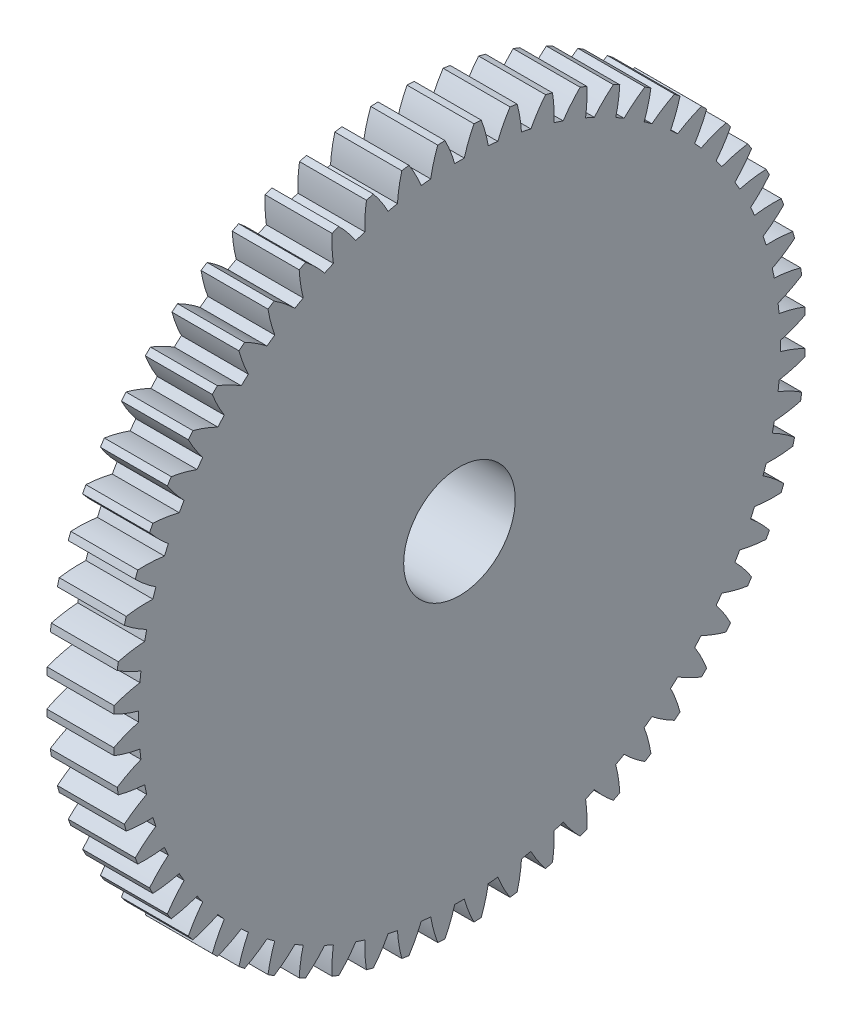
SolidWorks part; units mm, degrees
material "铜"
ref_plane "Plane1" through (0, 0, 0) normal (0, 0, 1) x (1, 0, 0)
ref_plane "Plane2" through (0, 0, 0) normal (0, 1, 0) x (1, 0, 0)
ref_plane "Plane3" through (0, 0, 0) normal (1, 0, 0) x (0, 0, -1)
sketch "HoldingSke" plane through (0, 0, 0) normal (0, 1, 0) x (1, 0, 0)
  line L0 (0, 0) -> (1, -1.7321)
  line L1 (-15, 0) -> (100, 0) construction
  line L2 (0, 0) -> (-2.1039, 2.3779)
  line L3 (0, 0) -> (-11.863, 4.5341)
  line L4 (0, 0) -> (4.318, 7.479)
  line L5 (0, 0) -> (-7.4956, -2.7956)
  line L6 (0, 0) -> (-2.4869, -1.6779)
  line L7 (-2.1039, 2.3779) -> (-0.3819, 10.1904)
  line L8 (-76.2, 54.61) -> (-75.3, 54.61)
  line L9 (-71.009, 38.7566) -> (-53.1078, 45.2721)
  line L10 (-76.2, 71.12) -> (104.1128, 71.12)
  line L11 (0, 0) -> (-3, 0)
  line L12 (-76.2, 101.6) -> (-76.181, 101.6)
  line L13 (24.9733, 27.94) -> (52.9518, 28.4284)
  line L14 (24.9733, 27.94) -> (24.9743, 27.94)
  line L15 (24.9733, 27.94) -> (100.4006, 29.5858)
  line L16 (-63.627, -0.5) -> (-12.827, -0.5)
  circle A0 centre (0, 0) radius 2.5
  circle A1 centre (0, 0) radius 4.5
  circle A2 centre (0, 0) radius 4.5
  circle A3 centre (0, 0) radius 2.5
  dimension "MHD" = 9
  dimension "Hub_dia" = 9
  dimension "Bore" = 5
  dimension "MBD" = 5
  dimension "Num_teeth" = 60
  dimension "Pitch" = 2
  dimension "Overall_len" = 8
  dimension "Show_teeth" = 60
  dimension "Thickness" = 3
  dimension "OAL" = 8.0001
  dimension "T_dim" = 0.9
  dimension "Ap" = 20
  dimension "H" = 19.05
  dimension "Pitch_radius" = 180.3128
  dimension "Width" = 3
  dimension "Backlash" = 0.019
  dimension "Addendum_fac" = 1
  dimension "Dedendum_fac" = 1.25
  dimension "Clearance_fac" = 0.25
  dimension "Dedendum_add" = 0.001
  dimension "Module" = 0.5
sketch "BasProSke" plane through (0, 0, 0) normal (0, 1, 0) x (1, 0, 0)
  line L0 (-10, 0) -> (60, 0) construction
  line L1 (0, 0) -> (0, 15.5)
  line L2 (0, 0) -> (3, 0)
  line L3 (3, 0) -> (3, 15.5)
  line L4 (3, 15.5) -> (0, 15.5)
  dimension "Thickness" = 3
  dimension "Diameter" = 31
revolve "Base-Revolve" add sketch "BasProSke" angle 360 about L0
sketch "TooCutSke" plane through (0, 0, 0) normal (1, 0, 0) x (0, 0, -1)
  line L1 (0, 0) -> (0, 107) construction
  line L2 (0, 0) -> (-0.4259, 14.994) construction
  line L3 (0, 0) -> (-1.5696, 29.9503) construction
  line L4 (-0.4259, 14.994) -> (-0.7848, 14.9751) construction
  arc A0 (0.2149, 14.3724) -> (-0.2149, 14.3724) centre (0, 0) ccw
  arc A1 (0.6627, 15.5112) -> (-0.6627, 15.5112) centre (0, 0) ccw
  circle A2 centre (0, 0) radius 15 construction
  circle A3 centre (0, 0) radius 14.0954 construction
  arc A4 (-0.2149, 14.3724) -> (-0.6627, 15.5112) centre (-5.9936, 12.7576) ccw
  arc A5 (0.6627, 15.5112) -> (0.2149, 14.3724) centre (5.9936, 12.7576) ccw
  dimension "Root_dia" = 28.748
  dimension "Overcut_dia" = 31.0508
  dimension "Pitch_dia" = 30
  dimension "Base_dia" = 28.1908
  dimension "Flank_rad" = 6
  dimension "Half_ang" = 3
  dimension "Half_CT" = 0.3594
extrude "ToothCut" cut sketch "TooCutSke" along normal through all
fillet "Breaks" [suppressed] radius 0.01
fillet "RootFillets" [suppressed] radius 0.126
pattern_circular "TeethCuts" count 60 every 6 about axis through (-10, 0, 0) along (1, 0, 0) of "ToothCut", "RootFillets", "Breaks"
sketch "HubNeaOneSke" plane through (0, 0, 0) normal (-1, 0, 0) x (0, 0, 1)
  circle A0 centre (0, 0) radius 4.5
  dimension "Diameter" = 9
extrude "HubNearOne" add sketch "HubNeaOneSke" along normal blind 5.0001
sketch "HubNeaBotSke" plane through (0, 0, 0) normal (-1, 0, 0) x (0, 0, 1)
  circle A0 centre (0, 0) radius 4.5
  dimension "Diameter" = 9
extrude "HubNearBoth" [suppressed] add sketch "HubNeaBotSke" along normal blind 2.5
ref_plane "FarPln" through (3, 0, 0) normal (1, 0, 0) x (0, 0, -1)
sketch "HubFarSke" plane through (3, 0, 0) normal (1, 0, 0) x (0, 0, -1)
  circle A0 centre (0, 0) radius 4.5
  dimension "Diameter" = 9
extrude "HubFar" [suppressed] add sketch "HubFarSke" along normal blind 2.5
sketch "BorSke" plane through (0, 0, 0) normal (1, 0, 0) x (0, 0, -1)
  circle A0 centre (0, 0) radius 2.5
  dimension "Diameter" = 5
extrude "Bore" cut sketch "BorSke" along normal mid plane 16.0001
sketch "KeySke" plane through (0, 0, 0) normal (1, 0, 0) x (0, 0, -1)
  line L0 (-1, 0) -> (-1, 3.4)
  line L1 (-1, 3.4) -> (1, 3.4)
  line L2 (1, 3.4) -> (1, 0)
  line L3 (0, 0) -> (0, 34) construction
  line L4 (-1, 0) -> (1, 0)
  dimension "Offset" = 3.4
  dimension "Width" = 2
extrude "Keyway" [suppressed] cut sketch "KeySke" along normal mid plane 16.0001
pattern_circular "Keyway2" [suppressed] count 2 every 90 about axis through (-10, 0, 0) along (1, 0, 0)
equation "' \"Module@HoldingSke\" = 6.35"
equation "' \"Num_teeth@HoldingSke\" = 12"
equation "' \"Ap@HoldingSke\" =  20"
equation "' \"Ap@HoldingSke\" = 20"
equation "' \"Width@HoldingSke\" = 0.5 * 25.4"
equation "' \"Hub_dia@HoldingSke\"= 1 * 25.4"
equation "' \"Hub_dia@HoldingSke\" = 1 * 25.4"
equation "' \"Overall_len@HoldingSke\" = 1.0 * 25.4"
equation "' \"Bore@HoldingSke\" = 0.75 * 25.4"
equation "' \"T_dim@HoldingSke\" = 0.1 * 25.4"
equation "' \"Width@KeySke\" = 0.25 * 25.4"
equation "' \"Show_teeth@HoldingSke\" = 13"
equation "' \"Backlash@HoldingSke\" = 0.009 * 25.4"
equation "' \"Addendum_fac@HoldingSke\" = 1.0"
equation "' \"Dedendum_fac@HoldingSke\" = 1.25"
equation "' \"Dedendum_add@HoldingSke\" = 0.00005 * 25.4"
equation "' \"Clearance_fac@HoldingSke\" = 0.25"
equation "\"Pitch@HoldingSke\" = 1 / \"Module@HoldingSke\""
equation "\"Overcut_dia@TooCutSke\" = (\"Num_teeth@HoldingSke\" + 2 * \"Addendum_fac@HoldingSke\") / \"Pitch@HoldingSke\" + 0.002 * 25.4"
equation "\"Pitch_dia@TooCutSke\" = \"Num_teeth@HoldingSke\" / \"Pitch@HoldingSke\""
equation "\"Base_dia@TooCutSke\" = \"Num_teeth@HoldingSke\" / \"Pitch@HoldingSke\" * cos((\"Ap@HoldingSke\"  * 3.14159265 / 180))"
equation "\"Root_dia@TooCutSke\" = (\"Num_teeth@HoldingSke\" + 2) / \"Pitch@HoldingSke\" - 2 * (\"Addendum_fac@HoldingSke\" + \"Dedendum_fac@HoldingSke\") / \"Pitch@HoldingSke\" - \"Dedendum_add@HoldingSke\" * 2"
equation "\"Half_ang@TooCutSke\" = 180 / \"Num_teeth@HoldingSke\""
equation "\"Half_CT@TooCutSke\" = \"Num_teeth@HoldingSke\" / \"Pitch@HoldingSke\" * sin((3.14159265 / 2 / \"Num_teeth@HoldingSke\")) / 2 - 7 * \"Backlash@HoldingSke\" / 4"
equation "\"Flank_rad@TooCutSke\" = \"Num_teeth@HoldingSke\" / \"Pitch@HoldingSke\" / 5"
equation "\"Radius@RootFillets\" = \"Clearance_fac@HoldingSke\" / \"Pitch@HoldingSke\" + \"Dedendum_add@HoldingSke\""
equation "\"Break_rad@Breaks\" = 0.02 / \"Pitch@HoldingSke\""
equation "\"Thickness@HoldingSke\" = \"Width@HoldingSke\""
equation "\"OAL@HoldingSke\" = \"Thickness@HoldingSke\""
equation "\"MHD@HoldingSke\" = (\"Num_teeth@HoldingSke\" + 2) / \"Pitch@HoldingSke\" - 2 * (\"Addendum_fac@HoldingSke\" + \"Dedendum_fac@HoldingSke\")  / \"Pitch@HoldingSke\" - \"Dedendum_add@HoldingSke\" * 2"
equation "\"MBD@HoldingSke\" = (\"Num_teeth@HoldingSke\" + 2) / \"Pitch@HoldingSke\" - 2 * (\"Addendum_fac@HoldingSke\" + \"Dedendum_fac@HoldingSke\")  / \"Pitch@HoldingSke\" - \"Dedendum_add@HoldingSke\" * 2 - 0.002 * 25.4"
equation "\"MHD@HoldingSke\" = ((sgn( \"MHD@HoldingSke\" - \"Hub_dia@HoldingSke\" )-1)*( \"MHD@HoldingSke\" - \"Hub_dia@HoldingSke\" ))/-2+ \"Hub_dia@HoldingSke\""
equation "\"MBD@HoldingSke\" = ((sgn( \"MBD@HoldingSke\" - \"Bore@HoldingSke\" )-1)*( \"MBD@HoldingSke\" - \"Bore@HoldingSke\" ))/-2+ \"Bore@HoldingSke\""
equation "\"OAL@HoldingSke\" = ((sgn( \"OAL@HoldingSke\" - \"Overall_len@HoldingSke\" )+1)*( \"OAL@HoldingSke\" - \"Overall_len@HoldingSke\" ))/2 + \"Overall_len@HoldingSke\" + 0.000002 * 25.4"
equation "\"Num_teeth@TeethCuts\" = int( \"Show_teeth@HoldingSke\" ) + 1"
equation "\"Num_teeth@TeethCuts\" = ((sgn( \"Num_teeth@TeethCuts\" - \"Num_teeth@HoldingSke\" )-1)*( \"Num_teeth@TeethCuts\" - \"Num_teeth@HoldingSke\" ))/-2+ \"Num_teeth@HoldingSke\""
equation "\"Num_teeth@TeethCuts\" = ((sgn( \"Num_teeth@TeethCuts\" - 2.0)+1)*( \"Num_teeth@TeethCuts\" - 2.0))/2 +2.0"
equation "\"Angle@TeethCuts\" = 360.0 / \"Num_teeth@HoldingSke\""
equation "\"Diameter@BasProSke\" = (\"Num_teeth@HoldingSke\" + 2 * \"Addendum_fac@HoldingSke\") / \"Pitch@HoldingSke\""
equation "\"Thickness@BasProSke\"  = \"Thickness@HoldingSke\""
equation "' \"Fillet_rad@BasProSke\" =  \"Thickness@HoldingSke\" * 0.05"
equation "' \"Fillet_rad@BasProSke\" = \"Thickness@HoldingSke\" * 0.05"
equation "\"MHD@HoldingSke\" = ((sgn( \"MHD@HoldingSke\" - \"Root_dia@TooCutSke\" )-1)*( \"MHD@HoldingSke\" - \"Root_dia@TooCutSke\" ))/-2+ \"Root_dia@TooCutSke\""
equation "\"Diameter@HubNeaOneSke\" = \"MHD@HoldingSke\""
equation "\"Length@HubNearOne\" = \"OAL@HoldingSke\" - \"Thickness@BasProSke\""
equation "\"Diameter@HubNeaBotSke\" = \"MHD@HoldingSke\""
equation "\"Length@HubNearBoth\" = ( \"OAL@HoldingSke\" - \"Thickness@BasProSke\" ) / 2.0"
equation "\"Thickness@FarPln\" = \"Thickness@BasProSke\""
equation "\"Diameter@HubFarSke\" = \"MHD@HoldingSke\""
equation "\"Length@HubFar\" = ( \"OAL@HoldingSke\" - \"Thickness@BasProSke\" ) / 2.0"
equation "\"Diameter@BorSke\" = \"MBD@HoldingSke\""
equation "\"D1@Bore\" = \"OAL@HoldingSke\" * 2.0"
equation "\"D1@Keyway\" = \"OAL@HoldingSke\" * 2.0"
equation "\"Offset@KeySke\" = \"T_dim@HoldingSke\" + \"MBD@HoldingSke\" / 2.0"
